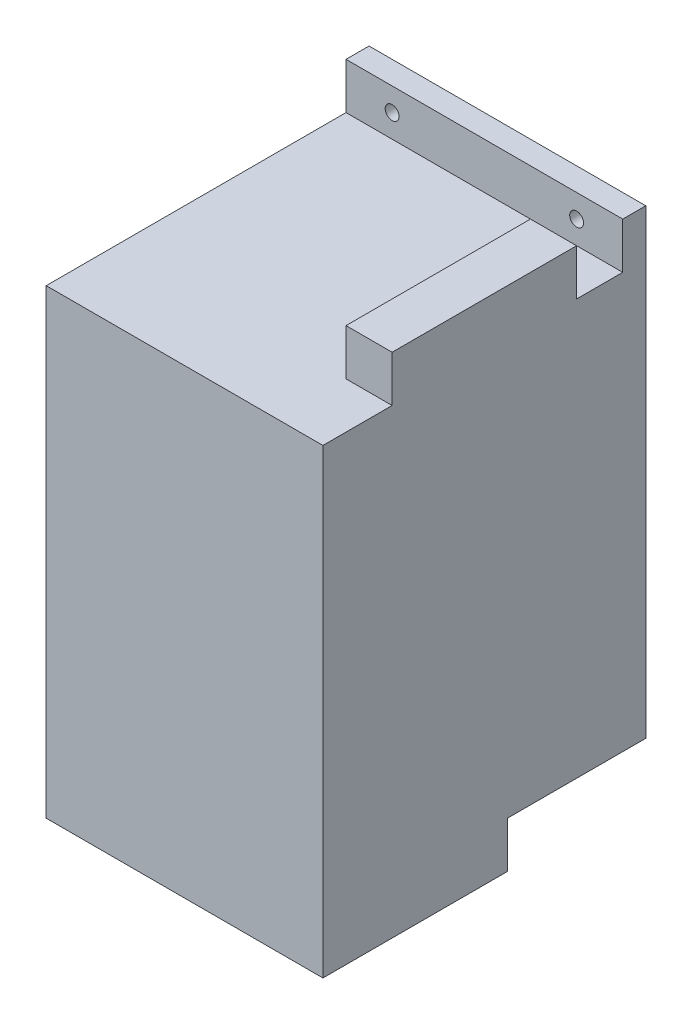
SolidWorks part; units mm, degrees
ref_plane "Front Plane" through (0, 0, 0) normal (0, 0, 1) x (1, 0, 0)
ref_plane "Top Plane" through (0, 0, 0) normal (0, 1, 0) x (1, 0, 0)
ref_plane "Right Plane" through (0, 0, 0) normal (1, 0, 0) x (0, 0, -1)
sketch "Sketch1" plane through (0, 0, 0) normal (0, 1, 0) x (1, 0, 0)
  line L1 (0, 0) -> (60, 0)
  line L2 (0, 0) -> (0, 70)
  line L3 (0, 70) -> (60, 70)
  line L4 (60, 0) -> (60, 70)
  dimension "D1" = 70
  dimension "D2" = 60
extrude "Boss-Extrude1" add sketch "Sketch1" along normal blind 100
sketch "Sketch2" plane through (0, 100, 0) normal (0, 1, 0) x (1, 0, 0)
  line L1 (50, 15) -> (60, 15)
  line L2 (50, 15) -> (50, 55)
  line L3 (50, 55) -> (60, 55)
  line L4 (60, 15) -> (60, 55)
  line L6 (60, 0) -> (60, 70) construction
  line L7 (60, 70) -> (0, 70) construction
  dimension "D1" = 10
  dimension "D2" = 15
  dimension "D3" = 40
extrude "Boss-Extrude2" add sketch "Sketch2" along normal blind 10
sketch "Sketch5" plane through (0, 100, 0) normal (0, 1, 0) x (1, 0, 0)
  line L0 (0, 70) -> (0, 0) construction
  line L1 (60, 70) -> (0, 70)
  line L2 (60, 70) -> (60, 65)
  line L3 (60, 65) -> (0, 65)
  line L4 (0, 70) -> (0, 65)
  dimension "D1" = 5
extrude "Boss-Extrude4" add sketch "Sketch5" along normal blind 10
sketch "Sketch6" plane through (0, 0, -70) normal (0, 0, -1) x (-1, 0, 0)
  line L0 (-60, 110) -> (-60, 0) construction
  line L1 (-60, 110) -> (0, 110) construction
  circle A0 centre (-50, 105) radius 1.5
  circle A1 centre (-10, 105) radius 1.5
  dimension "D1" = 40
  dimension "D4" = 3
  dimension "D5" = 3
  dimension "D2" = 10
  dimension "D3" = 5
extrude "Cut-Extrude4" cut sketch "Sketch6" against normal blind 10
sketch "Sketch7" plane through (0, 0, 0) normal (0, -1, 0) x (1, 0, 0)
  line L0 (60, -70) -> (0, -70) construction
  line L1 (60, -70) -> (0, -70)
  line L2 (60, -70) -> (60, -40)
  line L3 (60, -40) -> (0, -40)
  line L4 (0, -70) -> (0, -40)
  line L5 (0, -70) -> (0, 0) construction
  dimension "D1" = 30
extrude "Cut-Extrude5" cut sketch "Sketch7" against normal blind 10
